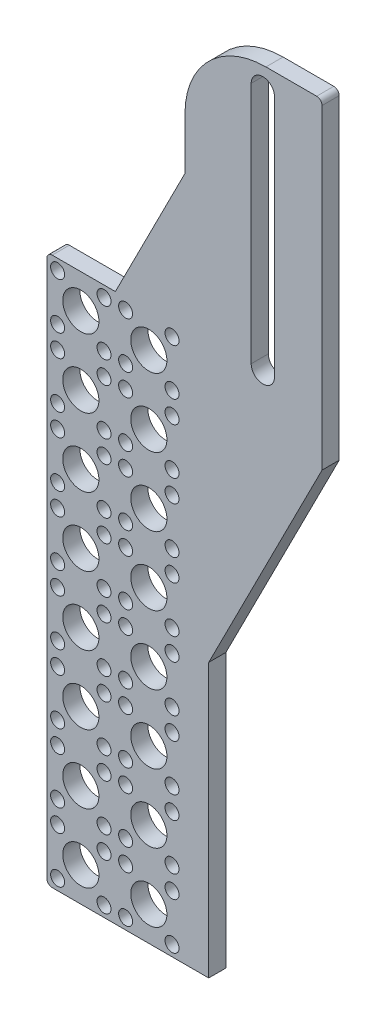
SolidWorks part; units mm, degrees
ref_plane "Front Plane" through (0, 0, 0) normal (0, 0, 1) x (1, 0, 0)
ref_plane "Top Plane" through (0, 0, 0) normal (0, 1, 0) x (1, 0, 0)
ref_plane "Right Plane" through (0, 0, 0) normal (1, 0, 0) x (0, 0, -1)
sketch "Reference Sketch" plane through (0, 0, 0) normal (0, 0, 1) x (1, 0, 0)
  line L0 (0, 0) -> (0, 25.019) construction
  line L1 (35.019, 0) -> (35.019, -50.019) construction
  line L2 (-1.725, 25.019) -> (1.725, 25.019)
  line L6 (35.019, -50.019) -> (-35.019, -50.019) construction
  line L7 (-35.019, 0) -> (-112.4213, 0) construction
  line L8 (-35.019, -50.019) -> (-35.019, 0) construction
  line L9 (0, -35.019) -> (0, -50.019) construction
  line L10 (-35.019, -50.019) -> (-75, -50.019)
  line L11 (35.019, 0) -> (112.4213, 0) construction
  line L12 (-75, -50.019) -> (-75, -120.019)
  line L13 (-75, -120.019) -> (75, -120.019)
  line L14 (75, -120.019) -> (75, -50.019)
  line L15 (35.019, -50.019) -> (75, -50.019)
  line L16 (0, 35.019) -> (70, 35.019)
  line L17 (70, 35.019) -> (70, -35.019)
  line L19 (0, 35.019) -> (-70, 35.019)
  line L20 (-70, 35.019) -> (-70, -35.019)
  line L22 (-35, -35.019) -> (-35.019, -50.019)
  line L23 (-128.24, -30) -> (-108.24, -30) construction
  line L24 (-128.24, -30) -> (-128.24, -140) construction
  line L25 (-128.24, -140) -> (-108.24, -140) construction
  line L26 (-108.24, -30) -> (-108.24, -140) construction
  line L27 (35.019, -50.019) -> (35, -35.019)
  line L28 (70, -35.019) -> (35, -35.019)
  line L29 (-50, -55.019) -> (50, -55.019) construction
  line L30 (-50, -55.019) -> (-50, -115.019) construction
  line L31 (-50, -115.019) -> (50, -115.019) construction
  line L32 (50, -55.019) -> (50, -115.019) construction
  line L33 (-35, -35.019) -> (-70, -35.019)
  circle A0 centre (0, 0) radius 25.019 construction
  circle A1 centre (0, 25.019) radius 1.725 construction
  circle A2 centre (17.6911, 17.6911) radius 1.725 construction
  circle A3 centre (25.019, 0) radius 1.725 construction
  circle A4 centre (17.6911, -17.6911) radius 1.725 construction
  circle A5 centre (0, -25.019) radius 1.725 construction
  circle A6 centre (-17.6911, -17.6911) radius 1.725 construction
  circle A7 centre (0, -82.931) radius 139.7 construction
  circle A8 centre (0, -82.931) radius 13.9065 construction
  circle A9 centre (0, 0) radius 35.019 construction
  circle A10 centre (-25.019, 0) radius 1.725 construction
  circle A11 centre (-17.6911, 17.6911) radius 1.725 construction
  circle A12 centre (0, 0) radius 2.16 construction
  circle A13 centre (-63.2127, 5.019) radius 2.16
  circle A14 centre (-63.2127, 5.019) radius 2.8702 construction
  circle A15 centre (-53.2127, 5.019) radius 2.16
  circle A16 centre (-53.2127, 5.019) radius 2.8702 construction
  circle A17 centre (-53.2127, -4.981) radius 2.16
  circle A18 centre (-53.2127, -4.981) radius 2.8702 construction
  circle A19 centre (-53.2127, -14.981) radius 2.16
  circle A20 centre (-53.2127, -14.981) radius 2.8702 construction
  circle A21 centre (-53.2127, -24.981) radius 2.16
  circle A22 centre (-53.2127, -24.981) radius 2.8702 construction
  circle A23 centre (-63.2127, -4.981) radius 2.16
  circle A24 centre (-63.2127, -4.981) radius 2.8702 construction
  circle A25 centre (-63.2127, -14.981) radius 2.16
  circle A26 centre (-63.2127, -14.981) radius 2.8702 construction
  circle A27 centre (-63.2127, -24.981) radius 2.16
  circle A28 centre (-63.2127, -24.981) radius 2.8702 construction
  point P23 (0, 56.769)
  point P52 (0, -115.019)
  point P54 (50, -85.019)
  point P56 (75, -85.019)
  point P63 (35.0095, -42.519)
  point P64 (0, -42.519)
  point P65 (0, 0)
  point P66 (0, 0)
  point P87 (0, 0)
  dimension "D1" = 50.038
  dimension "D2" = 3.45
  dimension "D5" = 279.4
  dimension "D10" = 27.813
  dimension "D12" = 10
  dimension "D19" = 4.32
  dimension "D21" = 70.038
  dimension "D22" = 50.038
  dimension "D23" = 4.32
  dimension "D24" = 5.7404
  dimension "D4" = 25.019
  dimension "D6" = 31.75
  dimension "D7" = 15
  dimension "D8" = 70
  dimension "D9" = 108.24
  dimension "D11" = 30
  dimension "D13" = 20
  dimension "D14" = 110
  dimension "D15" = 150
  dimension "D16" = 70
  dimension "D17" = 100
  dimension "D18" = 60
  dimension "D20" = 35
  dimension "D27" = 10
  dimension "D28" = 10
  dimension "D29" = 30
  dimension "D30" = 6.7873
  dimension "D25" = 2
  dimension "D26" = 4
  dimension "D3" = 8
sketch "Sketch2" plane through (0, 0, 0) normal (0, 0, 1) x (1, 0, 0)
  line L0 (-117.64, -34.181) -> (-126.24, -34.181) construction
  line L2 (-128.24, -32.181) -> (-128.24, -133.681)
  line L3 (-128.24, -133.681) -> (-98.24, -133.681)
  line L5 (-126.24, -34.181) -> (-126.24, -42.781) construction
  line L6 (-77.24, -32.181) -> (-77.24, -41.681)
  line L8 (-102.64, -32.181) -> (-102.64, 17.819)
  line L9 (-102.64, 17.819) -> (-77.24, 17.819)
  line L10 (-77.24, -32.181) -> (-77.24, 17.819)
  line L11 (-88.2127, 13.819) -> (-88.2127, -31.181) construction
  line L12 (-86.0527, 13.819) -> (-86.0527, -31.181)
  line L13 (-90.3727, 13.819) -> (-90.3727, -31.181)
  line L14 (-128.24, -32.181) -> (-77.24, -32.181)
  line L15 (0, -82.931) -> (139.7, -82.931) construction
  line L16 (-128.24, -30) -> (-128.24, -140) construction
  line L17 (-102.64, -6.781) -> (-115.54, -32.181)
  line L20 (-77.24, -41.681) -> (-98.24, -83.0298)
  line L21 (-77.24, -41.681) -> (-128.24, -41.681) construction
  line L22 (-98.24, -83.0298) -> (-98.24, -133.681)
  circle A0 centre (-126.24, -34.181) radius 1.2954
  circle A1 centre (-126.24, -42.781) radius 1.2954
  circle A2 centre (-121.94, -38.481) radius 3.35
  circle A3 centre (-117.64, -34.181) radius 1.2954
  circle A4 centre (-117.64, -42.781) radius 1.2954
  circle A5 centre (-105.04, -42.781) radius 1.2954
  circle A6 centre (-113.64, -42.781) radius 1.2954
  circle A7 centre (-109.34, -38.481) radius 3.35
  circle A8 centre (-105.04, -34.181) radius 1.2954
  circle A9 centre (-113.64, -34.181) radius 1.2954
  circle A10 centre (-105.04, -55.481) radius 1.2954
  circle A11 centre (-113.64, -55.481) radius 1.2954
  circle A12 centre (-109.34, -51.181) radius 3.35
  circle A13 centre (-105.04, -46.881) radius 1.2954
  circle A14 centre (-113.64, -46.881) radius 1.2954
  circle A15 centre (-105.04, -68.181) radius 1.2954
  circle A16 centre (-113.64, -68.181) radius 1.2954
  circle A17 centre (-109.34, -63.881) radius 3.35
  circle A18 centre (-105.04, -59.581) radius 1.2954
  circle A19 centre (-113.64, -59.581) radius 1.2954
  circle A20 centre (-105.04, -80.881) radius 1.2954
  circle A21 centre (-113.64, -80.881) radius 1.2954
  circle A22 centre (-109.34, -76.581) radius 3.35
  circle A23 centre (-105.04, -72.281) radius 1.2954
  circle A24 centre (-113.64, -72.281) radius 1.2954
  circle A25 centre (-105.04, -93.581) radius 1.2954
  circle A26 centre (-113.64, -93.581) radius 1.2954
  circle A27 centre (-109.34, -89.281) radius 3.35
  circle A28 centre (-105.04, -84.981) radius 1.2954
  circle A29 centre (-113.64, -84.981) radius 1.2954
  circle A30 centre (-105.04, -106.281) radius 1.2954
  circle A31 centre (-113.64, -106.281) radius 1.2954
  circle A32 centre (-109.34, -101.981) radius 3.35
  circle A33 centre (-105.04, -97.681) radius 1.2954
  circle A34 centre (-113.64, -97.681) radius 1.2954
  circle A35 centre (-105.04, -118.981) radius 1.2954
  circle A36 centre (-113.64, -118.981) radius 1.2954
  circle A37 centre (-109.34, -114.681) radius 3.35
  circle A38 centre (-105.04, -110.381) radius 1.2954
  circle A39 centre (-113.64, -110.381) radius 1.2954
  circle A40 centre (-105.04, -131.681) radius 1.2954
  circle A41 centre (-113.64, -131.681) radius 1.2954
  circle A42 centre (-109.34, -127.381) radius 3.35
  circle A43 centre (-105.04, -123.081) radius 1.2954
  circle A44 centre (-113.64, -123.081) radius 1.2954
  circle A45 centre (-117.64, -55.481) radius 1.2954
  circle A46 centre (-126.24, -55.481) radius 1.2954
  circle A47 centre (-121.94, -51.181) radius 3.35
  circle A48 centre (-117.64, -46.881) radius 1.2954
  circle A49 centre (-126.24, -46.881) radius 1.2954
  circle A50 centre (-117.64, -68.181) radius 1.2954
  circle A51 centre (-126.24, -68.181) radius 1.2954
  circle A52 centre (-121.94, -63.881) radius 3.35
  circle A53 centre (-117.64, -59.581) radius 1.2954
  circle A54 centre (-126.24, -59.581) radius 1.2954
  circle A55 centre (-117.64, -80.881) radius 1.2954
  circle A56 centre (-126.24, -80.881) radius 1.2954
  circle A57 centre (-121.94, -76.581) radius 3.35
  circle A58 centre (-117.64, -72.281) radius 1.2954
  circle A59 centre (-126.24, -72.281) radius 1.2954
  circle A60 centre (-117.64, -93.581) radius 1.2954
  circle A61 centre (-126.24, -93.581) radius 1.2954
  circle A62 centre (-121.94, -89.281) radius 3.35
  circle A63 centre (-117.64, -84.981) radius 1.2954
  circle A64 centre (-126.24, -84.981) radius 1.2954
  circle A65 centre (-117.64, -106.281) radius 1.2954
  circle A66 centre (-126.24, -106.281) radius 1.2954
  circle A67 centre (-121.94, -101.981) radius 3.35
  circle A68 centre (-117.64, -97.681) radius 1.2954
  circle A69 centre (-126.24, -97.681) radius 1.2954
  circle A70 centre (-117.64, -118.981) radius 1.2954
  circle A71 centre (-126.24, -118.981) radius 1.2954
  circle A72 centre (-121.94, -114.681) radius 3.35
  circle A73 centre (-117.64, -110.381) radius 1.2954
  circle A74 centre (-126.24, -110.381) radius 1.2954
  circle A75 centre (-117.64, -131.681) radius 1.2954
  circle A76 centre (-126.24, -131.681) radius 1.2954
  circle A77 centre (-121.94, -127.381) radius 3.35
  circle A78 centre (-117.64, -123.081) radius 1.2954
  circle A79 centre (-126.24, -123.081) radius 1.2954
  arc A80 (-86.0527, 13.819) -> (-90.3727, 13.819) centre (-88.2127, 13.819) ccw
  arc A81 (-90.3727, -31.181) -> (-86.0527, -31.181) centre (-88.2127, -31.181) ccw
  circle A82 centre (0, -82.931) radius 139.7 construction
  point P14 (-121.94, -34.181)
  point P15 (-126.24, -38.481)
  point P17 (-88.2127, -8.681)
  point P195 (-128.24, -82.931)
  dimension "D1" = 2.5908
  dimension "D3" = 6.7
  dimension "D10" = 2.16
  dimension "D2" = 8.6
  dimension "D4" = 25
  dimension "D5" = 2
  dimension "D6" = 101.5
  dimension "D7" = 2
  dimension "D9" = 9.5
  dimension "D11" = 2
  dimension "D12" = 50
  dimension "D13" = 25.4
  dimension "D14" = 4
  dimension "D15" = 45
  dimension "D16" = 4
  dimension "D17" = 12.7
  dimension "D18" = 25.4
  dimension "D19" = 21
  dimension "D21" = 30
extrude "Boss-Extrude1" add sketch "Sketch2" along normal blind 3.175
fillet "Fillet1" radius 15 1 edges at (-102.64, 17.819, 1.5875)
fillet "Fillet2" radius 1 3 edges at (-128.24, -133.681, 1.5875) (-128.24, -32.181, 1.5875) (-77.24, 17.819, 1.5875)
